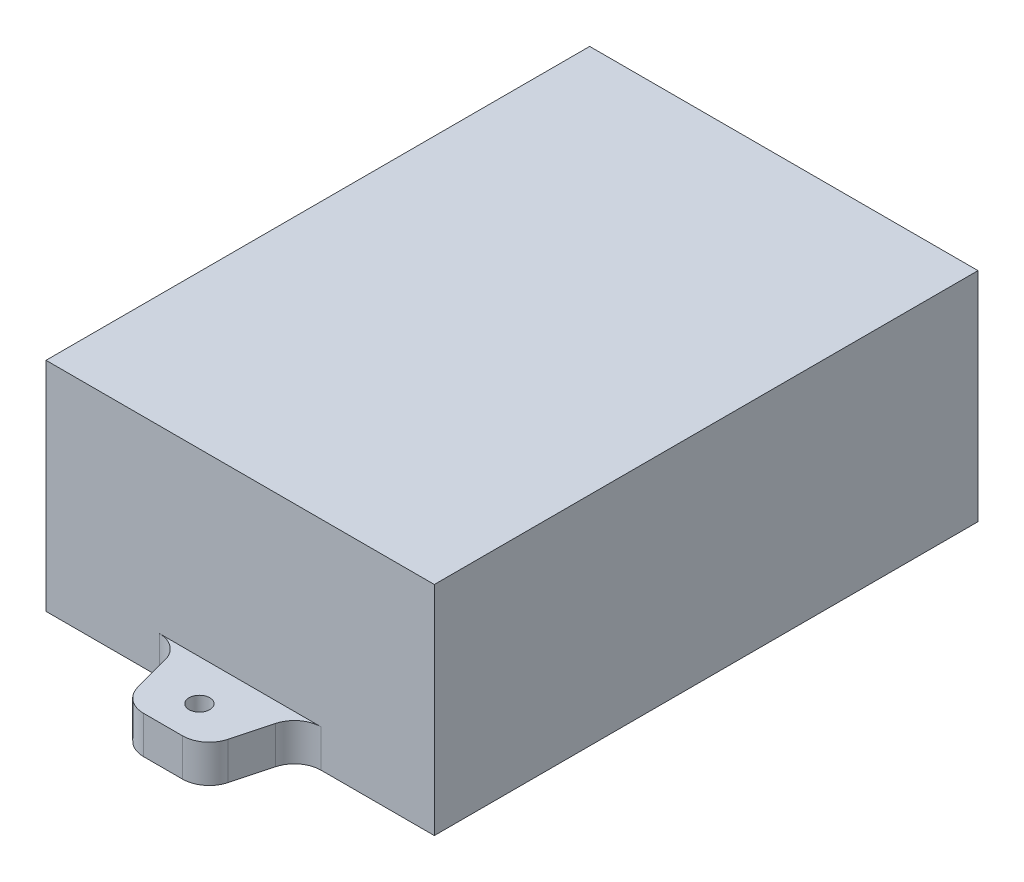
SolidWorks part; units mm, degrees
ref_plane "Front Plane" through (0, 0, 0) normal (0, 0, 1) x (1, 0, 0)
ref_plane "Top Plane" through (0, 0, 0) normal (0, 1, 0) x (1, 0, 0)
ref_plane "Right Plane" through (0, 0, 0) normal (1, 0, 0) x (0, 0, -1)
sketch "Sketch1" plane through (0, 0, 0) normal (0, 1, 0) x (1, 0, 0)
  line L1 (-30, -42) -> (30, -42)
  line L2 (-30, -42) -> (-30, 42)
  line L3 (-30, 42) -> (30, 42)
  line L4 (30, -42) -> (30, 42)
  line L5 (-30, -42) -> (30, 42) construction
  line L6 (-30, 42) -> (30, -42) construction
  point P0 (0, 0)
  dimension "D1" = 60
  dimension "D2" = 84
extrude "Boss-Extrude1" add sketch "Sketch1" along normal blind 33.6
sketch "Sketch2" plane through (0, 0, 0) normal (0, 1, 0) x (1, 0, 0)
  line L0 (-12.5, 42) -> (12.5, 42)
  line L2 (30, 42) -> (-30, 42) construction
  line L3 (-8.5275, 45.0482) -> (-6.9725, 50.8518)
  line L4 (-3, 53.9) -> (3, 53.9)
  line L5 (6.9725, 50.8518) -> (8.5275, 45.0482)
  line L6 (-30, 0) -> (30, 0) construction
  line L7 (-30, 42) -> (-30, -42) construction
  line L8 (30, -42) -> (30, 42) construction
  line L9 (6.9725, -50.8518) -> (8.5275, -45.0482)
  line L10 (-3, -53.9) -> (3, -53.9)
  line L11 (-8.5275, -45.0482) -> (-6.9725, -50.8518)
  line L12 (-12.5, -42) -> (12.5, -42)
  circle A0 centre (0, 48.3) radius 1.6
  arc A1 (-12.5, 42) -> (-8.5275, 45.0482) centre (-12.5, 46.1126) ccw
  arc A2 (-3, 53.9) -> (-6.9725, 50.8518) centre (-3, 49.7874) ccw
  arc A3 (3, 53.9) -> (6.9725, 50.8518) centre (3, 49.7874) cw
  arc A4 (8.5275, 45.0482) -> (12.5, 42) centre (12.5, 46.1126) ccw
  arc A5 (8.5275, -45.0482) -> (12.5, -42) centre (12.5, -46.1126) cw
  arc A6 (3, -53.9) -> (6.9725, -50.8518) centre (3, -49.7874) ccw
  arc A7 (-3, -53.9) -> (-6.9725, -50.8518) centre (-3, -49.7874) cw
  arc A8 (-12.5, -42) -> (-8.5275, -45.0482) centre (-12.5, -46.1126) cw
  circle A9 centre (0, -48.3) radius 1.6
  point P4 (0, 42)
  point P13 (0, 53.9)
  dimension "D1" = 3.2
  dimension "D2" = 25
  dimension "D3" = 75
  dimension "D4" = 75
  dimension "D5" = 6
  dimension "D6" = 11.9
  dimension "D7" = 5.6
extrude "Boss-Extrude2" add sketch "Sketch2" along normal blind 5.8
